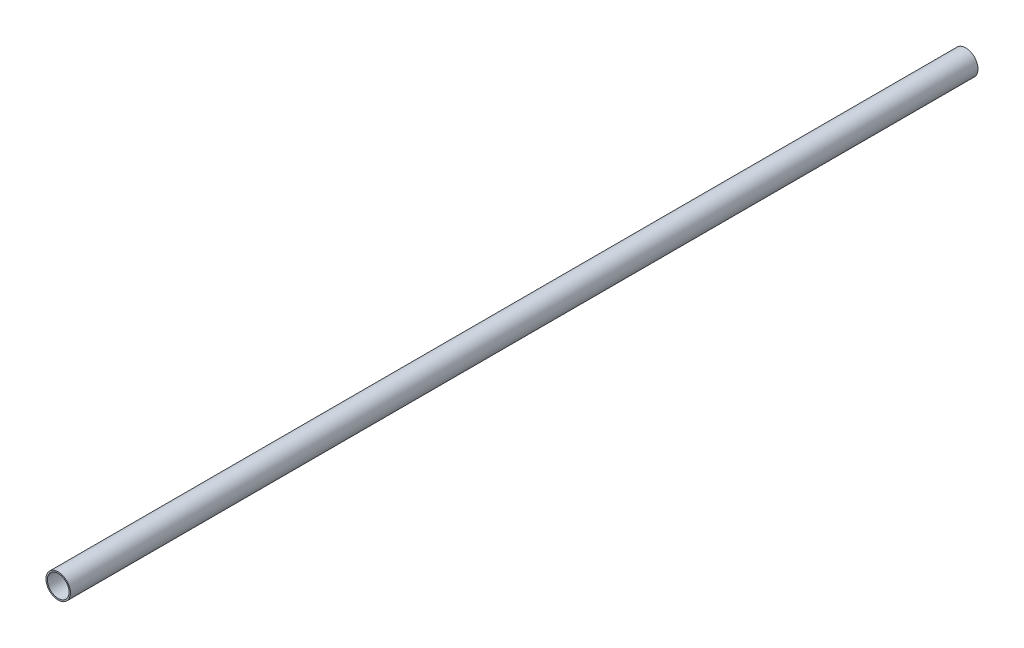
SolidWorks part; units mm, degrees
material "PVC Rigid"
ref_plane "Front Plane" through (0, 0, 0) normal (0, 0, 1) x (1, 0, 0)
ref_plane "Top Plane" through (0, 0, 0) normal (0, 1, 0) x (1, 0, 0)
ref_plane "Right Plane" through (0, 0, 0) normal (1, 0, 0) x (0, 0, -1)
sketch "Sketch1" plane through (0, 0, 0) normal (0, 0, 1) x (1, 0, 0)
  circle A0 centre (0, 0) radius 16.5926
  circle A2 centre (0, 0) radius 14.7257
  dimension "D1" = 33.1851
  dimension "D2" = 1.8669
extrude "Boss-Extrude1" add sketch "Sketch1" along normal blind 1231.9
